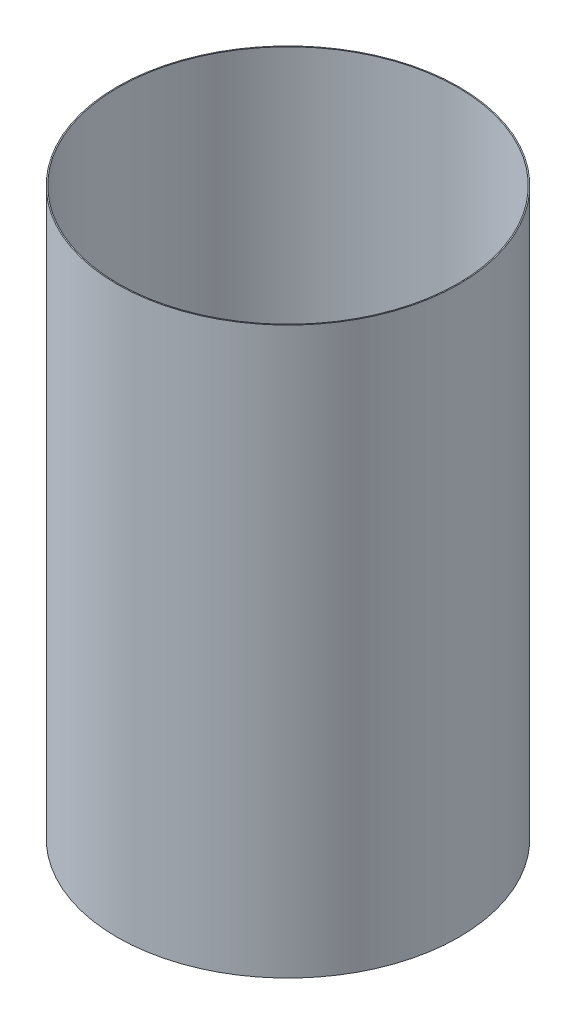
SolidWorks part; units mm, degrees
material "Thornel Mat VMA"
ref_plane "Front Plane" through (0, 0, 0) normal (0, 0, 1) x (1, 0, 0)
ref_plane "Top Plane" through (0, 0, 0) normal (0, 1, 0) x (1, 0, 0)
ref_plane "Right Plane" through (0, 0, 0) normal (1, 0, 0) x (0, 0, -1)
ref_axis "Axis1" through (0, 55, 0) along (0, -1, 0)
sketch "Sketch1" plane through (0, 0, 0) normal (0, 0, 1) x (1, 0, 0)
  line L0 (-40.0685, -69.0032) -> (-40.0685, -202.3532)
  line L2 (-38.1, -202.3532) -> (0, -202.3532) construction
  line L3 (-38.1, -69.0032) -> (0, -69.0032) construction
revolve "Revolve-Thin1" add sketch "Sketch1" angle 360 about axis through (0, 55, 0) along (0, -1, 0)
equation "\"D3@Revolve-Thin1\"=\"CF THICKNESS@Cryo Tank.Assembly\""
